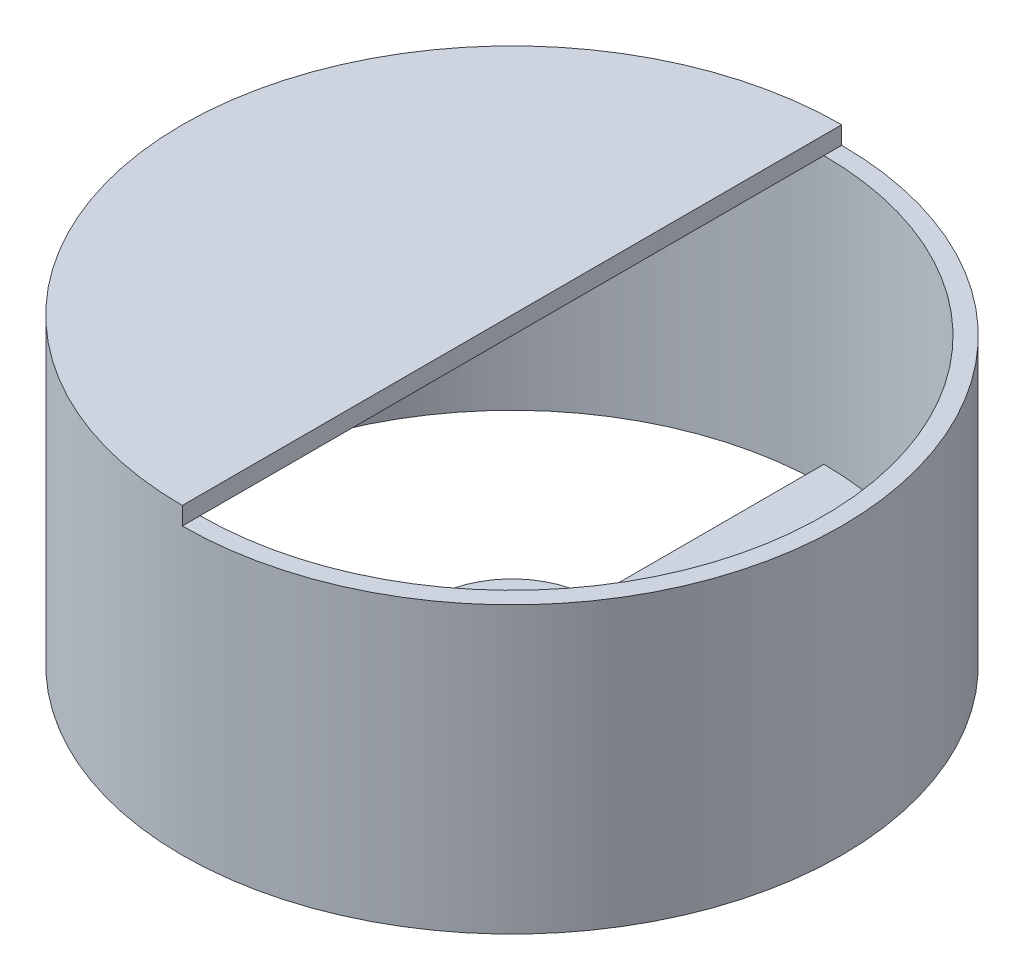
SolidWorks part; units mm, degrees
ref_plane "Front Plane" through (0, 0, 0) normal (0, 0, 1) x (1, 0, 0)
ref_plane "Top Plane" through (0, 0, 0) normal (0, 1, 0) x (1, 0, 0)
ref_plane "Right Plane" through (0, 0, 0) normal (1, 0, 0) x (0, 0, -1)
sketch "Sketch1" plane through (0, 0, 0) normal (0, 1, 0) x (1, 0, 0)
  line L0 (0, 4.5) -> (0, 17.5)
  line L1 (0, -4.5) -> (0, -17.5)
  circle A0 centre (0, 0) radius 18.5
  circle A1 centre (0, 0) radius 17.5
  circle A2 centre (0, 0) radius 3.5
  circle A3 centre (0, 0) radius 4.5
extrude "Boss-Extrude1" add sketch "Sketch1" along normal blind 1 contours A3 L1 A1 L0 | A3 A2 | A0 A1
sketch "Sketch2" plane through (0, 1, 0) normal (0, 1, 0) x (1, 0, 0)
  circle A0 centre (0, 0) radius 17.5
  circle A1 centre (0, 0) radius 18.5
extrude "Boss-Extrude2" add sketch "Sketch2" along normal blind 15
sketch "Sketch3" plane through (0, 16, 0) normal (0, 1, 0) x (1, 0, 0)
  line L0 (0, 18.5) -> (0, -18.5)
  circle A0 centre (0, 0) radius 18.5 construction
  arc A1 (0, 18.5) -> (0, -18.5) centre (0, 0) ccw
extrude "Boss-Extrude3" add sketch "Sketch3" along normal blind 1
